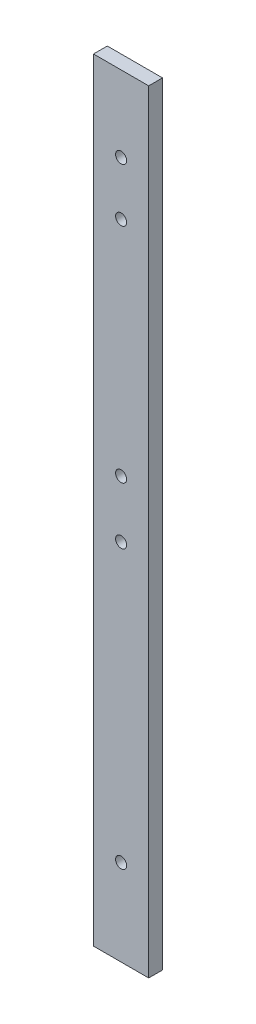
SolidWorks part; units mm, degrees
ref_plane "Front Plane" through (0, 0, 0) normal (0, 0, 1) x (1, 0, 0)
ref_plane "Top Plane" through (0, 0, 0) normal (0, 1, 0) x (1, 0, 0)
ref_plane "Right Plane" through (0, 0, 0) normal (1, 0, 0) x (0, 0, -1)
sketch "Sketch1" plane through (0, 0, 0) normal (0, 0, 1) x (1, 0, 0)
  line L1 (12.7, -177.8) -> (-12.7, -177.8)
  line L2 (12.7, -177.8) -> (12.7, 177.8)
  line L3 (12.7, 177.8) -> (-12.7, 177.8)
  line L4 (-12.7, -177.8) -> (-12.7, 177.8)
  line L5 (12.7, -177.8) -> (-12.7, 177.8) construction
  line L6 (12.7, 177.8) -> (-12.7, -177.8) construction
  point P0 (0, 0)
  dimension "D1" = 355.6
  dimension "D2" = 25.4
extrude "Boss-Extrude1" add sketch "Sketch1" along normal blind 6.35
sketch "Sketch2" plane through (0, 0, 6.35) normal (0, 0, 1) x (1, 0, 0)
  line L0 (0, 177.8) -> (0, -177.8) construction
  line L1 (12.7, 177.8) -> (-12.7, 177.8) construction
  line L2 (-12.7, -177.8) -> (12.7, -177.8) construction
  circle A0 centre (0, 142.875) radius 2.54
  circle A1 centre (0, 118.2687) radius 2.54
  circle A2 centre (0, 15.875) radius 2.54
  circle A3 centre (0, -10.3188) radius 2.54
  circle A4 centre (0, -138.1125) radius 2.54
  dimension "D6" = 5.08
  dimension "D1" = 34.925
  dimension "D2" = 59.5312
  dimension "D3" = 161.925
  dimension "D4" = 188.1188
  dimension "D5" = 315.9125
extrude "Cut-Extrude1" cut sketch "Sketch2" against normal through all
